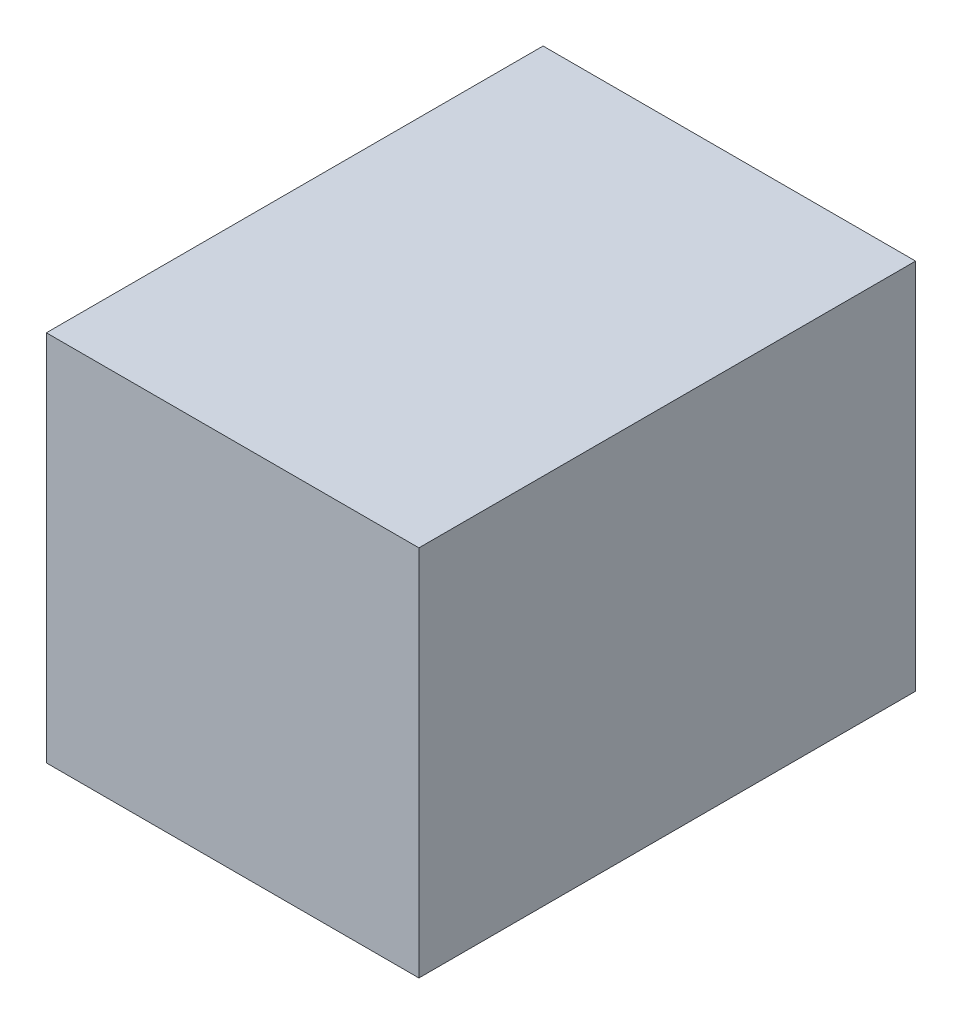
SolidWorks part; units mm, degrees
ref_plane "Plan de face" through (0, 0, 0) normal (0, 0, 1) x (1, 0, 0)
ref_plane "Plan de dessus" through (0, 0, 0) normal (0, 1, 0) x (1, 0, 0)
ref_plane "Plan de droite" through (0, 0, 0) normal (1, 0, 0) x (0, 0, -1)
sketch "Esquisse1" plane through (0, 0, 0) normal (0, 0, 1) x (1, 0, 0)
  line L1 (-101.8555, 24.5166) -> (-41.8555, 24.5166)
  line L2 (-101.8555, 24.5166) -> (-101.8555, -35.4834)
  line L3 (-101.8555, -35.4834) -> (-41.8555, -35.4834)
  line L4 (-41.8555, 24.5166) -> (-41.8555, -35.4834)
  dimension "D1" = 60
  dimension "D2" = 60
extrude "Boss.-Extru.1" add sketch "Esquisse1" along normal blind 80
equation "\"LargeurCharniere\"=60"
equation "\"D1@Esquisse1\"=\"LargeurCharniere\""
equation "\"EpaisseurPlaque\"= 10"
equation "\"ProfondeurPlacard\"=580"
equation "\"LargeurPlacard\"=160+70+135"
equation "\"DistanceAvantSyphon\"=240"
equation "\"DistanceAvantEvier\"=100"
equation "\"DiametreTuyau\"=90"
equation "\"HauteurTuyau\"=430"
equation "\"LargeurAeration\"=260"
equation "\"HauteurAeration\"=340"
equation "\"AerationSol\"=210"
equation "\"AerationAvant\"=270"
equation "\"ProfondeurCharniere\"=80"
equation "\"HauteurCharniere\"=60"
equation "\"HauteurPlacard\"=650"
equation "\"HauteurEvier\"=\"HauteurPlacard\"-555"
equation "\"HauteurDroitEvier\"=\"HauteurPlacard\" -500"
equation "\"HauteurSolSyphon\"=320"
equation "\"DiametreSyphon\"=70"
equation "\"PositionSyphonCoteGauche\"=160"
equation "\"D2@Esquisse1\"=\"HauteurCharniere\""
equation "\"D1@Boss.-Extru.1\"=\"ProfondeurCharniere\""
